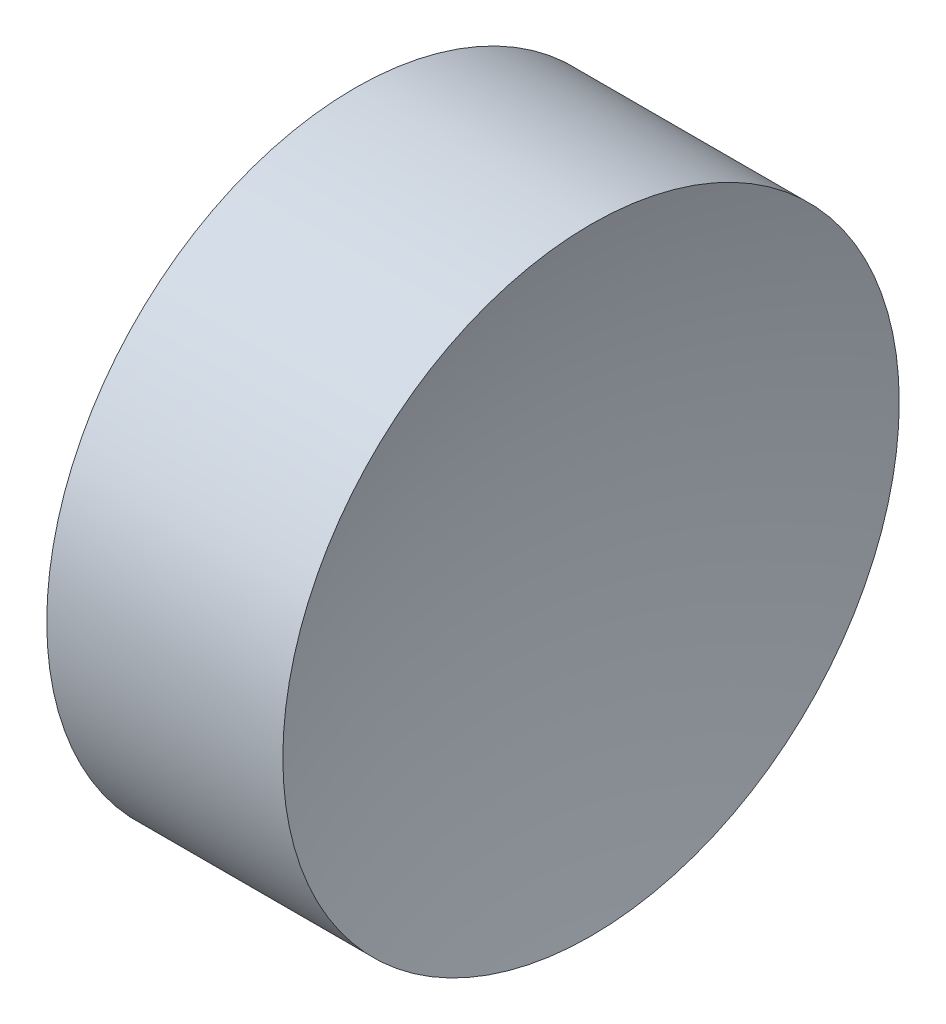
SolidWorks part; units mm, degrees
ref_plane "前视基准面" through (0, 0, 0) normal (0, 0, 1) x (1, 0, 0)
ref_plane "上视基准面" through (0, 0, 0) normal (0, 1, 0) x (1, 0, 0)
ref_plane "右视基准面" through (0, 0, 0) normal (1, 0, 0) x (0, 0, -1)
sketch "草图1" plane through (0, 0, 0) normal (0, 0, 1) x (1, 0, 0)
  line L0 (42.4499, 26.089) -> (55.6645, 26.089) construction
  line L1 (46.5452, 26.089) -> (49.5452, 26.089)
  line L3 (48.0452, 32.439) -> (50.4771, 32.439)
  line L4 (48.0452, 32.439) -> (45.6133, 32.439)
  arc A0 (50.4771, 32.439) -> (49.5452, 26.089) centre (71.6452, 26.089) ccw
  arc A1 (46.5452, 26.089) -> (45.6133, 32.439) centre (24.4452, 26.089) ccw
  dimension "D1" = 4.8638
  dimension "D2" = 3
revolve "旋转1" add sketch "草图1" angle 360 about L0
